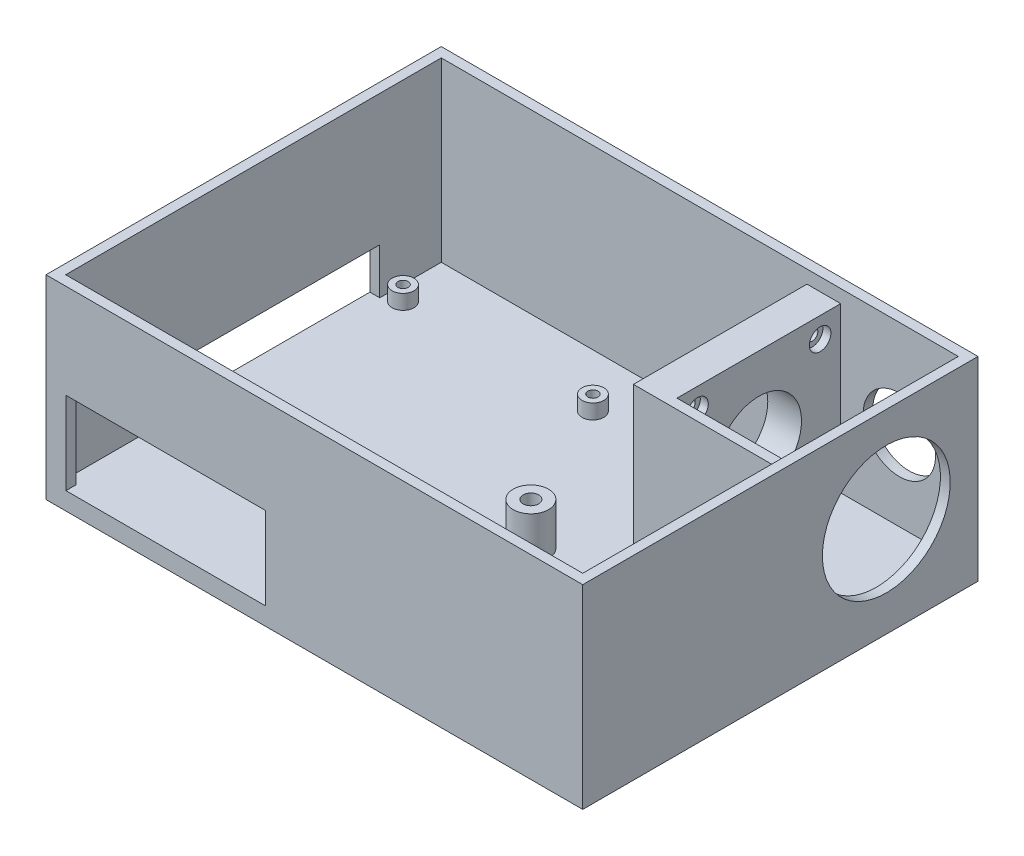
SolidWorks part; units mm, degrees
ref_plane "Front Plane" through (0, 0, 0) normal (0, 0, 1) x (1, 0, 0)
ref_plane "Top Plane" through (0, 0, 0) normal (0, 1, 0) x (1, 0, 0)
ref_plane "Right Plane" through (0, 0, 0) normal (1, 0, 0) x (0, 0, -1)
sketch "Sketch1" plane through (0, 0, 0) normal (0, 1, 0) x (1, 0, 0)
  line L1 (0, 0) -> (138.6427, 0)
  line L2 (0, 0) -> (0, 102.0986)
  line L3 (0, 102.0986) -> (138.6427, 102.0986)
  line L4 (138.6427, 0) -> (138.6427, 102.0986)
extrude "Boss-Extrude1" add sketch "Sketch1" along normal blind 4.572 contours L2 L1 L4 L3
sketch "Sketch2" plane through (0, 4.572, 0) normal (0, 1, 0) x (1, 0, 0)
  line L2 (0, 102.0986) -> (138.6427, 102.0986)
  line L4 (69.3214, 99.5586) -> (136.1027, 99.5586)
  line L5 (0, 102.0986) -> (0, 0)
  line L6 (136.1027, 99.5586) -> (136.1027, 51.0493)
  line L7 (0, 0) -> (138.6427, 0)
  line L9 (138.6427, 102.0986) -> (138.6427, 0)
  line L10 (2.54, 2.54) -> (136.1027, 2.54)
  line L11 (2.54, 2.54) -> (2.54, 99.5586)
  line L12 (2.54, 99.5586) -> (136.1027, 99.5586)
  line L13 (136.1027, 2.54) -> (136.1027, 99.5586)
  line L14 (2.54, 2.54) -> (136.1027, 99.5586) construction
  line L15 (2.54, 99.5586) -> (136.1027, 2.54) construction
  point P14 (69.3214, 51.0493)
  line M12 (138.6427, 102.0986) -> (0, 102.0986)
  line M13 (0, 102.0986) -> (0, 0)
  line M14 (0, 0) -> (138.6427, 0)
  line M15 (138.6427, 0) -> (138.6427, 102.0986)
extrude "Boss-Extrude2" add sketch "Sketch2" along normal blind 45.72 contours L13 L10 L11 L12 L4 L6 M15 M12 M13 M14
sketch "Sketch4" plane through (0, 0, 0) normal (-1, 0, 0) x (0, 0, 1)
  line L2 (-83.6676, 4.572) -> (-51.0493, 4.572)
  line L7 (-51.0493, 4.572) -> (-32.8676, 4.572)
  line L14 (-32.8676, 13.97) -> (-83.6676, 13.97)
  arc A0 (-83.6676, 13.97) -> (-83.6676, 4.572) centre (-78.9686, 9.271) ccw
  arc A1 (-32.8676, 13.97) -> (-32.8676, 4.572) centre (-37.5666, 9.271) cw
extrude "Cut-Extrude2" cut sketch "Sketch4" against normal blind 45.72 contours L2 L7 A1 L14 A0
sketch "Sketch5" plane through (0, 4.572, 0) normal (0, 1, 0) x (1, 0, 0)
  line L0 (2.54, 2.54) -> (2.54, 27.94)
  line L1 (2.54, 27.94) -> (6.3754, 27.94)
  line L2 (6.3754, 29.2608) -> (6.3754, 84.5312)
  line L3 (6.3754, 84.5312) -> (6.3754, 85.852)
  line L4 (7.6962, 27.94) -> (54.102, 27.94)
  line L5 (54.102, 27.94) -> (55.4228, 27.94)
  line L6 (6.3754, 85.852) -> (55.4228, 85.852)
  line L7 (55.4228, 85.852) -> (55.4228, 27.94)
  circle A0 centre (6.3754, 27.94) radius 1.3208
  circle A1 centre (6.3754, 27.94) radius 2.8194
  circle A2 centre (6.3754, 85.852) radius 1.3208
  circle A3 centre (6.3754, 85.852) radius 2.8194
  circle A4 centre (55.4228, 27.94) radius 1.3208
  circle A5 centre (55.4228, 27.94) radius 2.8194
  circle A6 centre (55.4228, 85.852) radius 1.3208
  circle A7 centre (55.4228, 85.852) radius 2.8194
extrude "Boss-Extrude3" add sketch "Sketch5" along normal blind 3.81 contours L4 A1 L2 A0 | L1 A1 L4 A0 | L2 A1 L1 A0 | L4 A5 L7 A4 | L7 A5 L4 A4 | L7 A7 L6 A6 | L6 A7 L7 A6 | L6 A3 L2 A2 | L2 A3 L6 A2
sketch "Sketch6" plane through (0, 4.572, 0) normal (0, 1, 0) x (1, 0, 0)
  circle A0 centre (6.3754, 27.94) radius 1.3208
  circle A1 centre (55.4228, 27.94) radius 1.3208
  circle A2 centre (55.4228, 85.852) radius 1.3208
  circle A3 centre (6.3754, 85.852) radius 1.3208
extrude "Cut-Extrude3" cut sketch "Sketch6" against normal blind 15.748
sketch "Sketch7" plane through (0, 0, 0) normal (0, -1, 0) x (1, 0, 0)
  circle A0 centre (6.3754, -27.94) radius 1.5494
  circle A1 centre (55.4228, -27.94) radius 1.5748
  circle A2 centre (55.4228, -85.852) radius 1.5748
  circle A3 centre (6.3754, -85.852) radius 1.5748
extrude "Cut-Extrude4" cut sketch "Sketch7" against normal blind 3.9878
sketch "Sketch9" plane through (0, 0, 0) normal (0, 0, 1) x (1, 0, 0)
  line L0 (0, 0) -> (0, 4.572)
  line L1 (0, 50.292) -> (0, 0) construction
  line L2 (0, 4.572) -> (2.54, 4.572)
  line L3 (2.54, 4.572) -> (5.1562, 4.572)
  line L4 (5.1562, 4.572) -> (5.1562, 25.908)
  line L5 (5.1562, 25.908) -> (56.7182, 25.908)
  line L6 (56.7182, 25.908) -> (56.7182, 4.572)
  line L7 (56.7182, 4.572) -> (5.1562, 4.572)
extrude "Cut-Extrude5" cut sketch "Sketch9" against normal blind 13.3858 contours L7 L6 L5 L4
sketch "Sketch10" plane through (0, 4.572, 0) normal (0, 1, 0) x (1, 0, 0)
  line L0 (56.7436, 85.852) -> (59.8424, 85.852)
  line L1 (56.7436, 27.94) -> (59.8424, 27.94)
  line L2 (59.8424, 85.852) -> (59.8424, 27.94)
  line L4 (59.8424, 85.852) -> (59.8424, 99.5586)
  line L5 (2.54, 99.5586) -> (136.1027, 99.5586) construction
  line L9 (97.0026, 57.2676) -> (97.0026, 99.5586)
  line L10 (97.0026, 57.2676) -> (59.8424, 57.2676)
  line L11 (97.0026, 57.2676) -> (105.7148, 57.2676)
  line L12 (105.7148, 57.2676) -> (105.7148, 99.5586)
  line L13 (2.54, 99.5586) -> (136.1027, 99.5586) construction
  line L14 (105.7148, 99.5586) -> (97.0026, 99.5586)
  circle A0 centre (55.4228, 85.852) radius 1.3208 construction
  circle A1 centre (55.4228, 27.94) radius 1.3208 construction
  line M11 (136.1027, 99.5586) -> (2.54, 99.5586)
extrude "Boss-Extrude4" add sketch "Sketch10" along normal blind 42.3418 contours L11 L12 L9 M11
sketch "Sketch11" plane through (105.7148, 0, 0) normal (1, 0, 0) x (0, 0, -1)
  line L0 (99.5586, 46.9138) -> (57.2676, 4.572)
  line L1 (99.5586, 4.572) -> (57.2676, 46.9138)
  circle A0 centre (78.4131, 25.7429) radius 11.0236
extrude "Cut-Extrude6" cut sketch "Sketch11" against normal blind 42.3418 contours L0 A0 L1 | L1 A0 L0 | L0 A0 L1 | L1 A0 L0
sketch "Sketch12" plane through (105.7148, 0, 0) normal (1, 0, 0) x (0, 0, -1)
  line L28 (64.0367, 9.8806) -> (92.7895, 9.8806)
  line L29 (62.5762, 11.3411) -> (62.5762, 40.1447)
  line L30 (64.0367, 41.6052) -> (92.7895, 41.6052)
  line L31 (94.25, 11.3411) -> (94.25, 40.1447)
  circle A4 centre (62.5762, 41.6052) radius 1.4605
  circle A5 centre (94.25, 9.8806) radius 1.4605
  circle A6 centre (62.5762, 9.8806) radius 1.4605
  circle A7 centre (94.25, 41.6052) radius 1.4605
extrude "Cut-Extrude9" cut sketch "Sketch12" against normal blind 42.3418 contours A5 | A6 | A7 | A4
sketch "Sketch15" plane through (105.7148, 0, 0) normal (1, 0, 0) x (0, 0, -1)
  circle A0 centre (62.5762, 41.6052) radius 2.7813
  circle A1 centre (94.25, 41.6052) radius 2.7813
  circle A2 centre (62.5762, 9.8806) radius 2.7813
  circle A3 centre (94.25, 9.8806) radius 2.7813
extrude "Cut-Extrude10" cut sketch "Sketch15" against normal blind 2.0574 contours A0 | A1 | A3 | A2
sketch "Sketch16" plane through (0, 4.572, 0) normal (0, 1, 0) x (1, 0, 0)
  line L0 (136.1027, 2.54) -> (136.1027, 99.5586) construction
  line L1 (97.0026, 57.2676) -> (136.1027, 57.2676)
  line L2 (97.0026, 57.2676) -> (97.0026, 54.7276)
  line L3 (97.0026, 54.7276) -> (136.1027, 54.7276)
  line L4 (136.1027, 57.2676) -> (136.1027, 54.7276)
extrude "Boss-Extrude5" add sketch "Sketch16" along normal up to surface (42.3418 mm away) up to face at (101.3587, 46.9138, -78.4131)
sketch "Sketch17" plane through (0, 4.572, 0) normal (0, 1, 0) x (1, 0, 0)
  circle A0 centre (78.0746, 47.1693) radius 1.4478
  circle A1 centre (115.438, 47.1693) radius 1.4478
  circle A2 centre (115.438, 9.8059) radius 1.4478
  circle A3 centre (78.0746, 9.8059) radius 1.4478
extrude "Cut-Extrude11" cut sketch "Sketch17" against normal blind 15.0114
sketch "Sketch18" plane through (0, 4.572, 0) normal (0, 1, 0) x (1, 0, 0)
  circle A0 centre (78.0746, 47.1693) radius 2.667
  circle A1 centre (78.0746, 47.1693) radius 1.4478
  circle A2 centre (115.438, 47.1693) radius 2.667
  circle A3 centre (115.438, 47.1693) radius 1.4478
  circle A4 centre (115.438, 9.8059) radius 1.4478
  circle A5 centre (115.438, 9.8059) radius 2.667
  circle A6 centre (78.0746, 9.8059) radius 2.667
  circle A7 centre (78.0746, 9.8059) radius 1.4478
extrude "Boss-Extrude6" add sketch "Sketch18" along normal blind 10.922
sketch "Sketch19" plane through (0, 15.494, 0) normal (0, 1, 0) x (1, 0, 0)
  circle A0 centre (115.438, 9.8059) radius 2.0193
  circle A1 centre (78.0746, 9.8059) radius 2.0193
  circle A2 centre (115.438, 47.1693) radius 2.0193
  circle A3 centre (78.0746, 47.1693) radius 2.0193
extrude "Cut-Extrude12" cut sketch "Sketch19" against normal blind 6.2738
sketch "Sketch20" plane through (0, 15.494, 0) normal (0, 1, 0) x (1, 0, 0)
  circle A0 centre (78.0746, 9.8059) radius 2.0193
  circle A1 centre (78.0746, 9.8059) radius 4.572
  circle A2 centre (115.438, 9.8059) radius 2.0193
  circle A3 centre (115.438, 9.8059) radius 4.572
  circle A4 centre (115.438, 47.1693) radius 2.0193
  circle A5 centre (115.438, 47.1693) radius 4.572
  circle A6 centre (78.0746, 47.1693) radius 2.0193
  circle A7 centre (78.0746, 47.1693) radius 4.572
extrude "Boss-Extrude7" add sketch "Sketch20" against normal up to surface (10.922 mm away) up to face at (115.438, 4.572, -7.1389)
sketch "Sketch21" plane through (97.0026, 0, 0) normal (-1, 0, 0) x (0, 0, 1)
  circle A0 centre (-78.4131, 25.7429) radius 11.0236
extrude "Cut-Extrude13" cut sketch "Sketch21" against normal blind 46.1518
ref_plane "Plane1" through (105.7148, 46.9138, -99.5586) normal (-1, 0, 0) x (0, 0, 1)
sketch "Sketch23" plane through (105.7148, 0, 0) normal (1, 0, 0) x (0, 0, -1)
  circle A0 centre (78.4131, 25.7429) radius 16.51
extrude "Cut-Extrude14" cut sketch "Sketch23" along normal blind 61.1378
sketch "Sketch25" plane through (0, 0, -102.0986) normal (0, 0, -1) x (-1, 0, 0)
  line L0 (-138.6427, 0) -> (-136.1027, 0)
  line L1 (0, 0) -> (-138.6427, 0) construction
  line L2 (-136.1027, 0) -> (-105.6227, 0)
  line L3 (-136.1027, 0) -> (-136.1027, 50.292)
  line L4 (-138.6427, 50.292) -> (0, 50.292) construction
  line L5 (-136.1027, 50.292) -> (-105.6227, 50.292)
  line L6 (-105.6227, 50.292) -> (-105.6227, 0)
  line L7 (-136.1027, 25.146) -> (-105.6227, 25.146)
  circle A0 centre (-120.8627, 25.146) radius 9.3597
extrude "Cut-Extrude15" cut sketch "Sketch25" against normal blind 15.1638 contours L7 A0 | L7 A0
ref_plane "Plane2" through (5.1562, 25.908, 0) normal (0, 1, 0) x (1, 0, 0)
sketch "Sketch27" plane through (0, 0, 0) normal (-1, 0, 0) x (0, 0, 1)
  line L0 (-32.8676, 13.97) -> (-32.8676, 4.572)
  line L2 (-83.6676, 4.572) -> (-32.8676, 4.572)
  line L3 (-83.6676, 4.572) -> (-83.6676, 16.4414)
  line L4 (-83.6676, 16.4414) -> (-32.8676, 16.4414)
  line L5 (-32.8676, 4.572) -> (-32.8676, 16.4414)
  line M2 (-83.6676, 13.97) -> (-32.8676, 13.97)
extrude "Cut-Extrude16" cut sketch "Sketch27" against normal blind 15.1638 contours L5 L4 L3 M2
sketch "Sketch28" plane through (0, 0, 0) normal (-1, 0, 0) x (0, 0, 1)
  line L0 (-83.6676, 4.572) -> (-83.6676, 13.97)
  arc A0 (-83.6676, 13.97) -> (-83.6676, 4.572) centre (-78.9686, 9.271) ccw
extrude "Boss-Extrude8" add sketch "Sketch28" against normal up to surface (2.54 mm away) up to face at (2.54, 17.9695, -55.3803)
sketch "Sketch29" plane through (0, 0, 0) normal (-1, 0, 0) x (0, 0, 1)
  line L0 (-32.8676, 13.97) -> (-32.8676, 4.572)
  arc A0 (-32.8676, 13.97) -> (-32.8676, 4.572) centre (-37.5666, 9.271) cw
extrude "Boss-Extrude9" add sketch "Sketch29" against normal up to surface (2.54 mm away) up to face at (2.54, 18.4139, -52.021)
